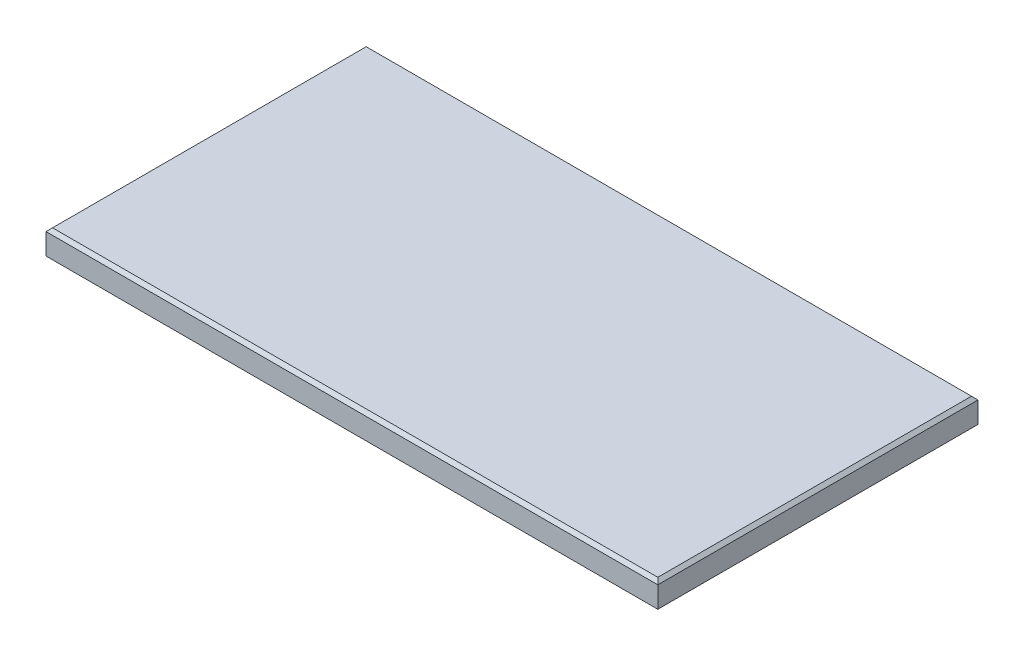
SolidWorks part; units mm, degrees
material "Oak"
ref_plane "Front Plane" through (0, 0, 0) normal (0, 0, 1) x (1, 0, 0)
ref_plane "Top Plane" through (0, 0, 0) normal (0, 1, 0) x (1, 0, 0)
ref_plane "Right Plane" through (0, 0, 0) normal (1, 0, 0) x (0, 0, -1)
sketch "Sketch1" plane through (0, 0, 0) normal (0, 1, 0) x (1, 0, 0)
  line L1 (0, 0) -> (476.25, 0)
  line L2 (0, 0) -> (0, 249.2375)
  line L3 (0, 249.2375) -> (476.25, 249.2375)
  line L4 (476.25, 0) -> (476.25, 249.2375)
  dimension "D1" = 249.2375
  dimension "D2" = 476.25
extrude "Boss-Extrude1" add sketch "Sketch1" along normal blind 19.05
chamfer "Chamfer1" distance 2.54 angle 45 4 edges at (238.125, 19.05, -249.2375) (476.25, 19.05, -124.6188) (238.125, 19.05, 0) (0, 19.05, -124.6188)
